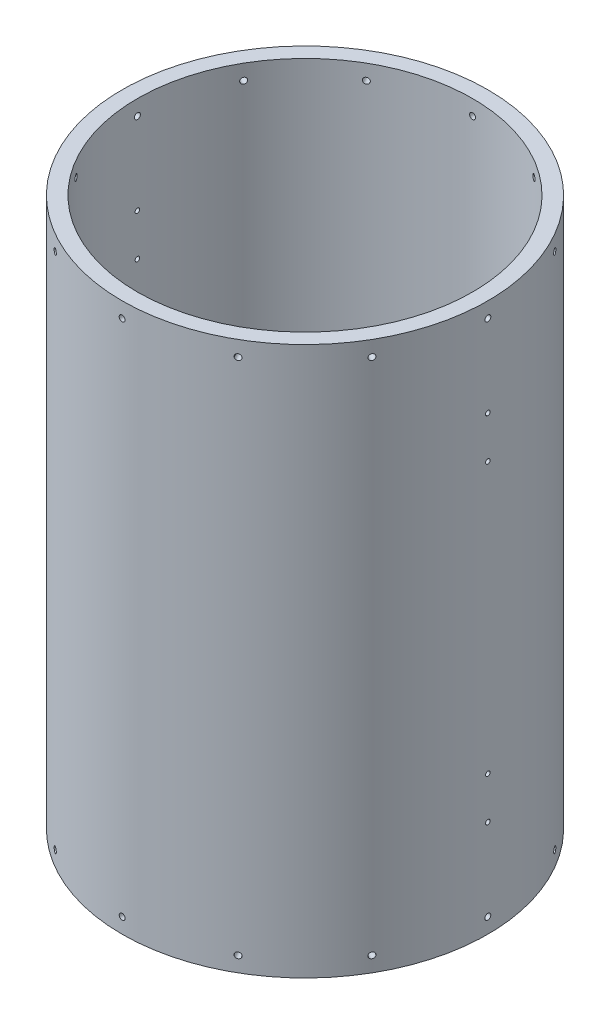
SolidWorks part; units mm, degrees
ref_plane "Front Plane" through (0, 0, 0) normal (0, 0, 1) x (1, 0, 0)
ref_plane "Top Plane" through (0, 0, 0) normal (0, 1, 0) x (1, 0, 0)
ref_plane "Right Plane" through (0, 0, 0) normal (1, 0, 0) x (0, 0, -1)
sketch "Sketch1" plane through (0, 0, 0) normal (0, 1, 0) x (1, 0, 0)
  circle A0 centre (0, 0) radius 152.4
  circle A1 centre (0, 0) radius 139.7
  dimension "D1" = 304.8
  dimension "D2" = 279.4
extrude "Boss-Extrude1" add sketch "Sketch1" along normal blind 457.2
ref_plane "Plane1" through (-152.4, 0, 0) normal (-1, 0, 0) x (0, 0, 1)
hole_wizard "#10 (0.1935) Diameter Hole1" positions "Sketch2" profile "Sketch3" hole size "#10" standard "ANSI Inch"
sketch "Sketch2" plane through (-152.4, 0, 0) normal (-1, 0, 0) x (0, 0, 1)
  line L0 (0, -167.64) -> (0, 167.64) construction
  line L1 (139.7, 457.2) -> (-139.7, 457.2) construction
  point P0 (0, 444.5)
  dimension "D1" = 12.7
sketch "Sketch3" plane through (-152.4, 444.5, 0) normal (0, 1, 0) x (0, 0, 1)
  line L0 (0, 0) -> (0, 343.2351)
  line L1 (0, 343.2351) -> (2.4574, 343.2351)
  line L2 (2.4574, 343.2351) -> (2.4574, 0)
  line L5 (2.4574, 0) -> (0, 0)
  line L11 (0, -6.35) -> (0, 107.95) construction
  dimension "Thru Hole Dia." = 4.9149
  dimension "Thru Hole Depth" = 343.2351
pattern_circular "CirPattern1" count 12 over 360 about axis through (0, 457.2, 0) along (0, -1, 0) of "#10 (0.1935) Diameter Hole1"
ref_plane "Plane2" through (0, 228.6, 0) normal (0, 1, 0) x (1, 0, 0)
mirror "Mirror1" about plane through (0, 228.6, 0) normal (0, 1, 0) of "CirPattern1", "#10 (0.1935) Diameter Hole1"
hole_wizard "#10-24 Tapped Hole1" positions "Sketch4" profile "Sketch5" tap size "#10-24" standard "ANSI Inch"
sketch "Sketch4" plane through (-152.4, 0, 0) normal (-1, 0, 0) x (0, 0, 1)
  line L0 (0, 341.3125) -> (0, 115.8875) construction
  line L2 (167.64, 228.6) -> (-167.64, 228.6) construction
  point P0 (0, 376.2375)
  point P2 (0, 341.3125)
  point P4 (0, 115.8875)
  point P6 (0, 80.9625)
  point P13 (0, 228.6)
  dimension "D1" = 260.35
  dimension "D2" = 34.925
  dimension "D3" = 34.925
sketch "Sketch5" plane through (-152.4, 376.2375, 0) normal (0, 1, 0) x (0, 0, 1)
  line L0 (0, 0) -> (0, 14.0948)
  line L1 (0, 14.0948) -> (1.8986, 12.954)
  line L2 (1.8986, 12.954) -> (1.8986, 0)
  line L5 (1.8986, 0) -> (0, 0)
  line L10 (0, 14.0948) -> (-1.8986, 12.954) construction
  line L11 (0, -6.35) -> (0, 107.95) construction
  dimension "Tap Drill Dia." = 3.7973
  dimension "Tap Drill Depth" = 12.954
  dimension "Drill Angle" = 118
cosmetic thread "Hole Thread1" parameters "D1"=9.652, "D2"=4.826
cosmetic thread "Hole Thread2" parameters "D1"=9.652, "D2"=4.826
cosmetic thread "Hole Thread3" parameters "D1"=9.652, "D2"=4.826
cosmetic thread "Hole Thread4" parameters "D1"=9.652, "D2"=4.826
pattern_circular "CirPattern2" count 2 over 360 about axis through (0, 457.2, 0) along (0, 1, 0) of "#10-24 Tapped Hole1"
equation "\"D3@Sketch4\"=\"D2@Sketch4\""
